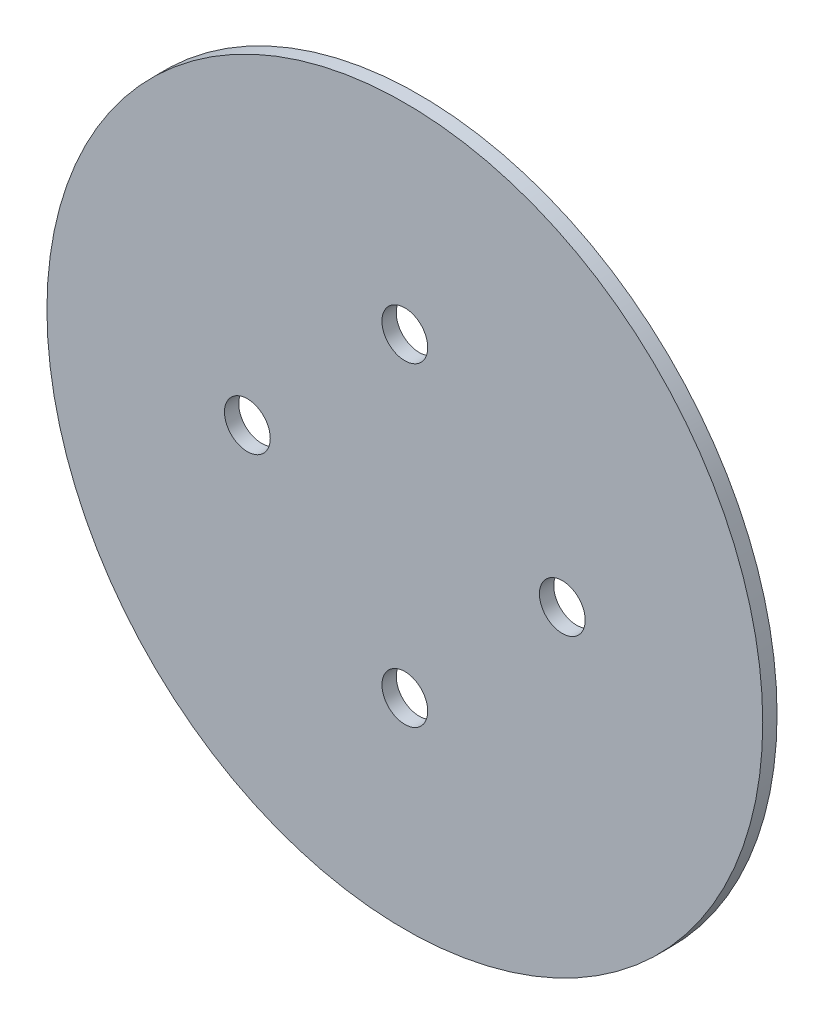
SolidWorks part; units mm, degrees
ref_plane "Front Plane" through (0, 0, 0) normal (1, 0, 0) x (0, 1, 0)
ref_plane "Top Plane" through (0, 0, 0) normal (0, 0, 1) x (0, 1, 0)
ref_plane "Right Plane" through (0, 0, 0) normal (0, 1, 0) x (-1, 0, 0)
sketch "Sketch1" plane through (0, 0, 0) normal (0, 0, 1) x (0, 1, 0)
  circle A0 centre (0, 0) radius 25
  circle A1 centre (0, 0) radius 11 construction
  circle A2 centre (0, 11) radius 1.6
  circle A3 centre (11, 0) radius 1.6
  circle A4 centre (0, -11) radius 1.6
  circle A5 centre (-11, 0) radius 1.6
  point P15 (0, 0)
  dimension "D1" = 50
  dimension "D2" = 22
  dimension "D3" = 3.2
  dimension "D4" = 4
extrude "Boss-Extrude1" add sketch "Sketch1" along normal blind 1
